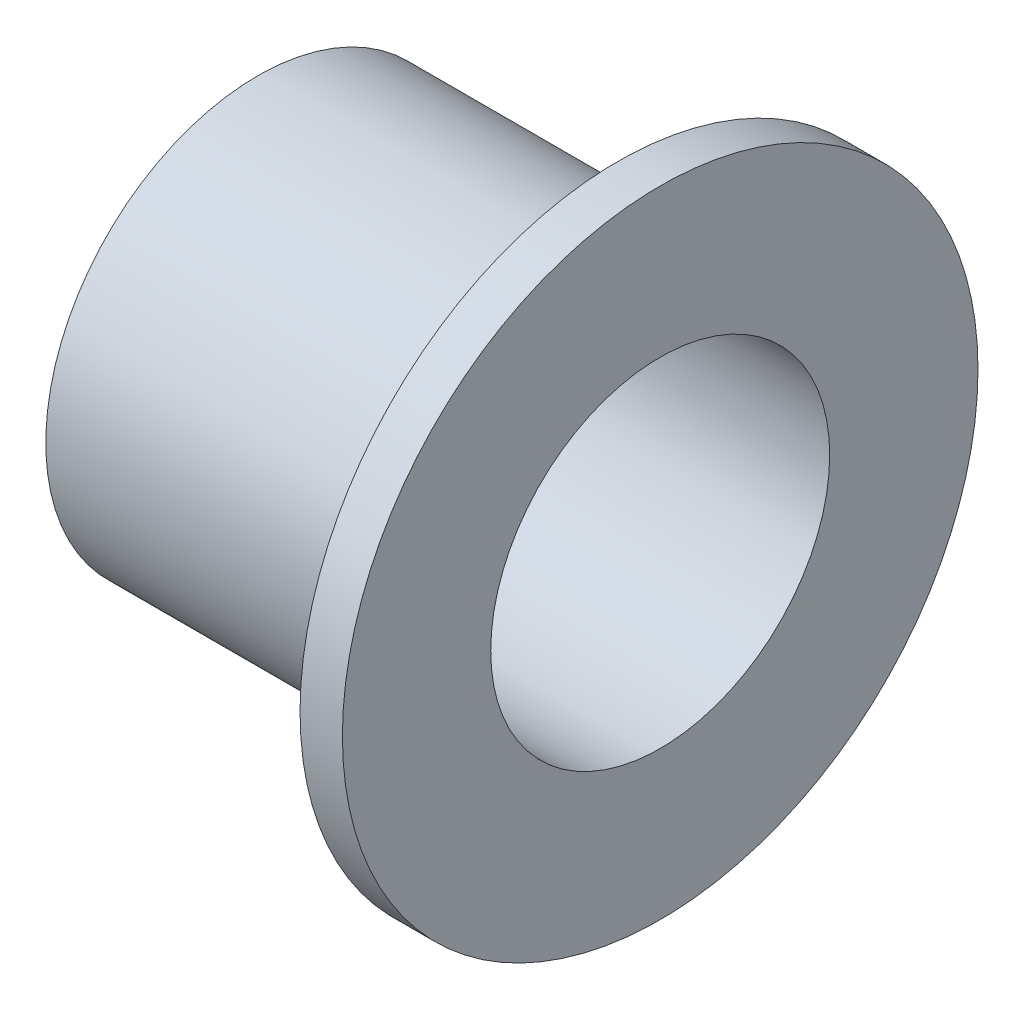
SolidWorks part; units mm, degrees
material "Stal stopowa"
ref_plane "Płaszczyzna przednia" through (0, 0, 0) normal (0, 0, 1) x (1, 0, 0)
ref_plane "Płaszczyzna górna" through (0, 0, 0) normal (0, 1, 0) x (1, 0, 0)
ref_plane "Płaszczyzna prawa" through (0, 0, 0) normal (1, 0, 0) x (0, 0, -1)
sketch "Szkic1" plane through (0, 0, 0) normal (1, 0, 0) x (0, 0, -1)
  circle A0 centre (0, 0) radius 4
  circle A1 centre (0, 0) radius 5
  dimension "D1" = 8
  dimension "D2" = 10
extrude "Dodanie-wyciągnięcie1" add sketch "Szkic1" along normal blind 8.5
sketch "Szkic2" plane through (8.5, 0, 0) normal (1, 0, 0) x (0, 0, -1)
  circle A0 centre (0, 0) radius 7.5
  circle A2 centre (0, 0) radius 4
extrude "Dodanie-wyciągnięcie3" add sketch "Szkic2" along normal blind 1
